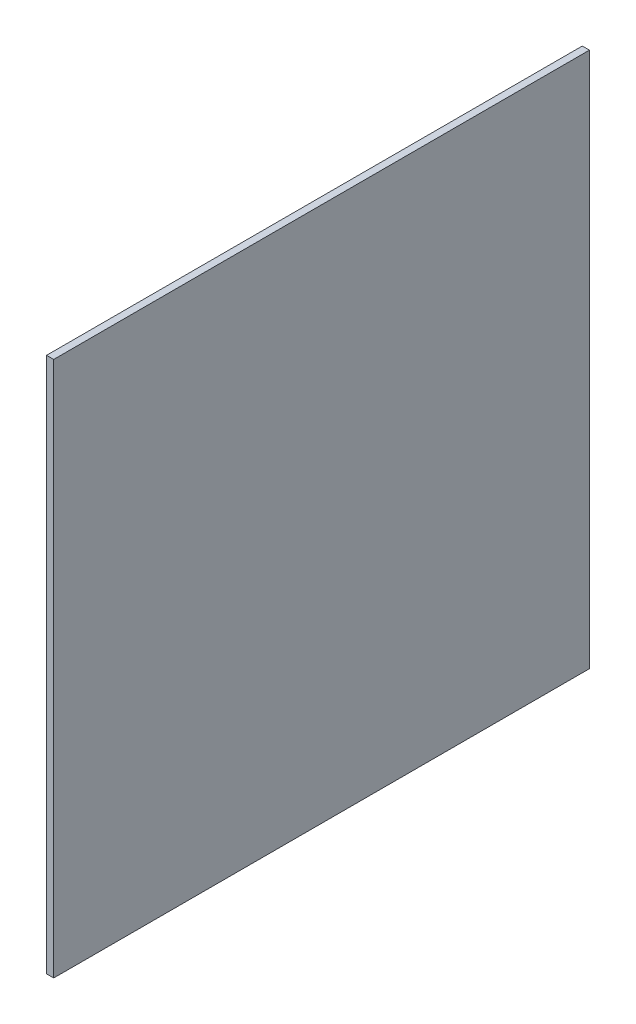
SolidWorks part; units mm, degrees
ref_plane "Front Plane" through (0, 0, 0) normal (0, 0, 1) x (1, 0, 0)
ref_plane "Top Plane" through (0, 0, 0) normal (0, 1, 0) x (1, 0, 0)
ref_plane "Right Plane" through (0, 0, 0) normal (1, 0, 0) x (0, 0, -1)
sketch "Sketch1" plane through (0, 0, 0) normal (0, 0, 1) x (1, 0, 0)
  line L1 (75, 75) -> (-75, 75) construction
  line L2 (-75, -75) -> (-73, -75)
  line L3 (-75, -75) -> (-75, 75)
  line L4 (-75, 75) -> (-73, 75)
  line L5 (-73, -75) -> (-73, 75)
  dimension "D1" = 2
extrude "Boss-Extrude1" add sketch "Sketch1" along normal blind 150
